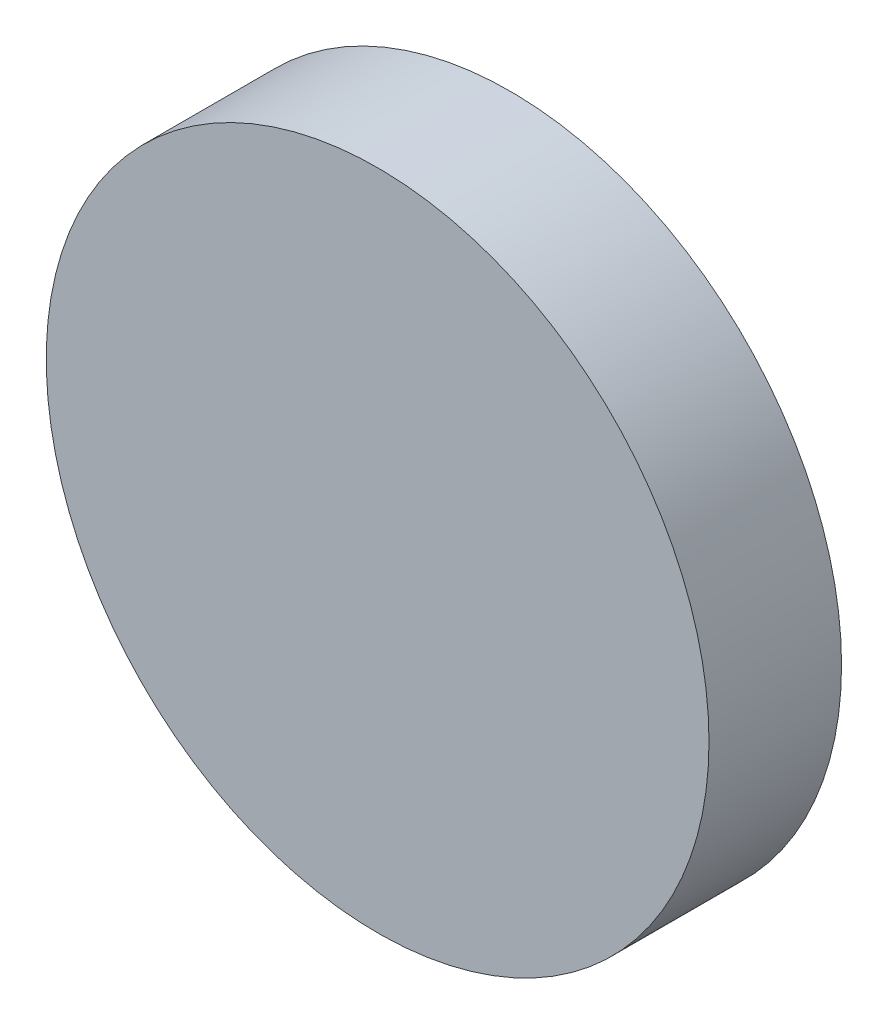
SolidWorks part; units mm, degrees
ref_plane "Plano frontal" through (0, 0, 0) normal (0, 0, 1) x (1, 0, 0)
ref_plane "Plano superior" through (0, 0, 0) normal (0, 1, 0) x (1, 0, 0)
ref_plane "Plano direito" through (0, 0, 0) normal (1, 0, 0) x (0, 0, -1)
sketch "Esboço1" plane through (0, 0, 0) normal (0, 0, 1) x (1, 0, 0)
  circle A0 centre (0, 0) radius 100
  dimension "D1" = 200
extrude "Ressalto-extrusão1" add sketch "Esboço1" along normal blind 40
